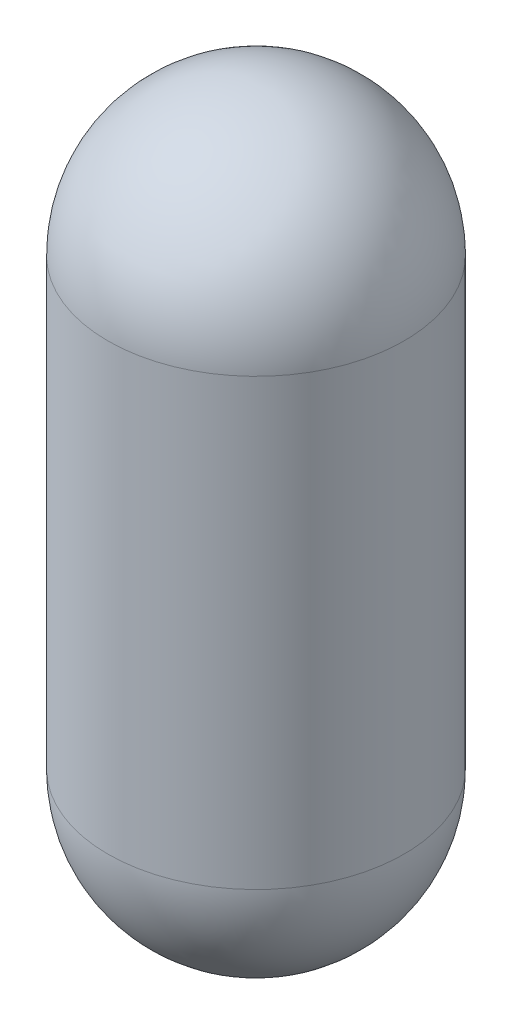
SolidWorks part; units mm, degrees
ref_plane "Front Plane" through (0, 0, 0) normal (0, 0, 1) x (1, 0, 0)
ref_plane "Top Plane" through (0, 0, 0) normal (0, 1, 0) x (1, 0, 0)
ref_plane "Right Plane" through (0, 0, 0) normal (1, 0, 0) x (0, 0, -1)
sketch "Sketch1" plane through (0, 0, 0) normal (0, 1, 0) x (1, 0, 0)
  circle A0 centre (0, 0) radius 25.4
  dimension "D1" = 50.8
extrude "Boss-Extrude1" add sketch "Sketch1" along normal blind 127
fillet "Fillet1" radius 25.4 2 edges at (0, 0, 25.4) (0, 127, 25.4)
